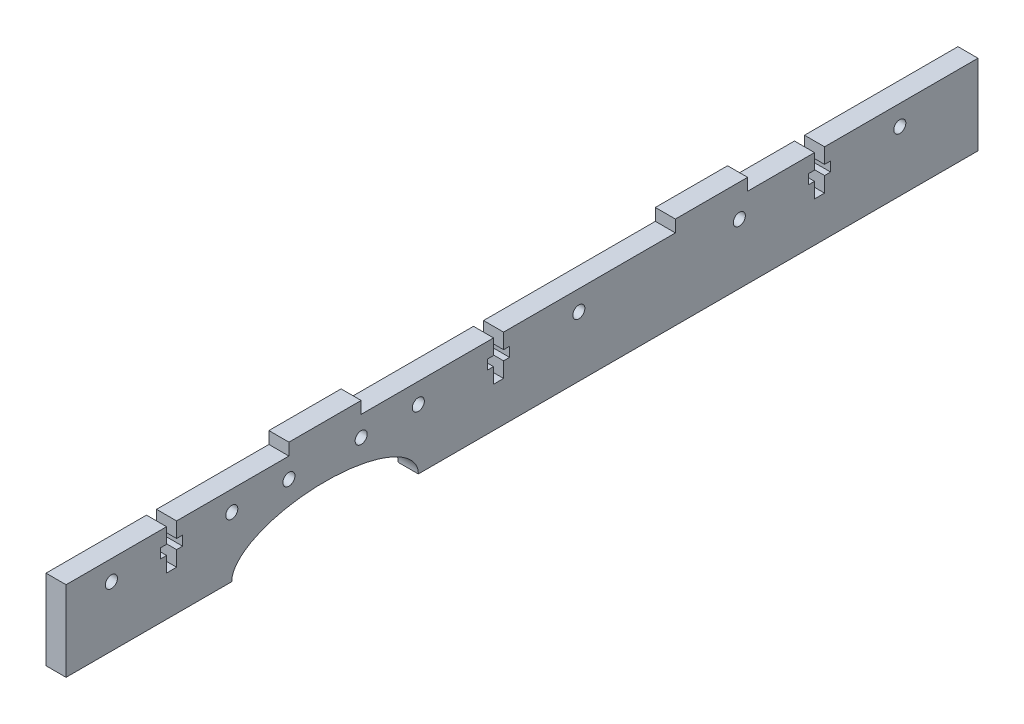
SolidWorks part; units mm, degrees
material "PMMA"
ref_plane "Front Plane" through (0, 0, 0) normal (0, 0, 1) x (1, 0, 0)
ref_plane "Top Plane" through (0, 0, 0) normal (0, 1, 0) x (1, 0, 0)
ref_plane "Right Plane" through (0, 0, 0) normal (1, 0, 0) x (0, 0, -1)
sketch "Schizzo1" plane through (0, 0, 0) normal (1, 0, 0) x (0, 0, -1)
  line L0 (-115.445, 5) -> (-2.745, 5) construction
  line L1 (-113.645, -10) -> (113.645, -10)
  line L2 (-113.645, -10) -> (-113.645, 10)
  line L3 (-113.645, 10) -> (-58.095, 10)
  line L4 (113.645, -10) -> (113.645, 10)
  line L5 (-49.095, 10) -> (-49.095, -10) construction
  line L6 (-58.095, 10) -> (-58.095, 13)
  line L7 (-58.095, 13) -> (-40.095, 13)
  line L8 (-40.095, 13) -> (-40.095, 10)
  line L9 (-40.095, 10) -> (113.645, 10)
  line L10 (-113.645, 10) -> (113.645, -10) construction
  point P8 (0, 0)
  dimension "D2" = 20
  dimension "D3" = 9
  dimension "D4" = 9
  dimension "D5" = 3
  dimension "D1" = 55.55
  dimension "D6" = 5
  dimension "D8" = 153.74
extrude "Estrusione-Estrusione1" add sketch "Schizzo1" along normal blind 5
sketch "Schizzo3" plane through (0, 0, 0) normal (1, 0, 0) x (0, 0, -1)
  line L1 (-40.095, 13) -> (-58.095, 13) construction
  line L2 (-113.645, -10) -> (113.645, -10) construction
  line L4 (-49.095, 13) -> (-49.095, -10) construction
  line L5 (-113.645, 5) -> (113.645, 5) construction
  line L10 (-58.095, 10) -> (-113.645, 10) construction
  line L11 (-113.645, 10) -> (-113.645, -10) construction
  line L12 (113.645, -10) -> (113.645, 10) construction
  circle A0 centre (-58.095, 5) radius 1.5
  circle A1 centre (-72.345, 5) radius 1.5
  circle A2 centre (-40.095, 5) radius 1.5
  circle A3 centre (-25.845, 5) radius 1.5
  circle A4 centre (14.155, 5) radius 1.5
  circle A5 centre (54.155, 5) radius 1.5
  circle A6 centre (94.155, 5) radius 1.5
  circle A7 centre (-102.345, 5) radius 1.5
  ellipse E0 centre (-49.095, -10) end of major axis (-25.845, -10) minor radius 10
  dimension "D3" = 3
  dimension "D6" = 3
  dimension "D4" = 4
  dimension "D1" = 9
  dimension "D2" = 23.25
  dimension "D5" = 2
  dimension "D8" = 5
extrude "Taglio-Estrusione1" cut sketch "Schizzo3" along direction (-1, 0, 0) on the side of the normal through all
sketch "Schizzo5" plane through (0, 0, 0) normal (1, 0, 0) x (0, 0, -1)
  line L0 (-100.845, 5) -> (-73.845, 5) construction
  line L1 (-24.345, 5) -> (12.655, 5) construction
  line L2 (55.655, 5) -> (92.655, 5) construction
  line L3 (-5.845, 0) -> (-5.845, 10) construction
  line L4 (-87.345, 0) -> (-87.345, 10) construction
  line L5 (-88.595, 0) -> (-88.595, 3.8)
  line L6 (-88.595, 3.8) -> (-90.095, 3.8)
  line L7 (-90.095, 3.8) -> (-90.095, 6.2)
  line L8 (-90.095, 6.2) -> (-88.595, 6.2)
  line L9 (-88.595, 6.2) -> (-88.595, 10)
  line L10 (-88.595, 10) -> (-86.095, 10)
  line L11 (-86.095, 10) -> (-86.095, 6.2)
  line L12 (-86.095, 6.2) -> (-84.595, 6.2)
  line L13 (-84.595, 6.2) -> (-84.595, 3.8)
  line L14 (-84.595, 3.8) -> (-86.095, 3.8)
  line L15 (-86.095, 3.8) -> (-86.095, 0)
  line L16 (-86.095, 0) -> (-88.595, 0)
  line L17 (-58.095, 10) -> (-113.645, 10) construction
  line L18 (-7.095, 0) -> (-7.095, 3.8)
  line L19 (-7.095, 3.8) -> (-8.595, 3.8)
  line L20 (-8.595, 3.8) -> (-8.595, 6.2)
  line L21 (-8.595, 6.2) -> (-7.095, 6.2)
  line L22 (-7.095, 6.2) -> (-7.095, 10)
  line L23 (-7.095, 10) -> (-4.595, 10)
  line L24 (-4.595, 10) -> (-4.595, 6.2)
  line L25 (-4.595, 6.2) -> (-3.095, 6.2)
  line L26 (-3.095, 6.2) -> (-3.095, 3.8)
  line L27 (-3.095, 3.8) -> (-4.595, 3.8)
  line L28 (-4.595, 3.8) -> (-4.595, 0)
  line L29 (-4.595, 0) -> (-7.095, 0)
  line L30 (113.645, 10) -> (-40.095, 10) construction
  line L31 (74.155, 0) -> (74.155, 10) construction
  line L32 (72.905, 0) -> (72.905, 3.8)
  line L33 (72.905, 3.8) -> (71.405, 3.8)
  line L34 (71.405, 3.8) -> (71.405, 6.2)
  line L35 (71.405, 6.2) -> (72.905, 6.2)
  line L36 (72.905, 6.2) -> (72.905, 10)
  line L37 (72.905, 10) -> (75.405, 10)
  line L38 (75.405, 10) -> (75.405, 6.2)
  line L39 (75.405, 6.2) -> (76.905, 6.2)
  line L40 (76.905, 6.2) -> (76.905, 3.8)
  line L41 (76.905, 3.8) -> (75.405, 3.8)
  line L42 (75.405, 3.8) -> (75.405, 0)
  line L43 (75.405, 0) -> (72.905, 0)
  line L44 (113.645, 10) -> (-40.095, 10) construction
  line L45 (-113.645, 10) -> (-113.645, -10) construction
  circle A0 centre (-102.345, 5) radius 1.5 construction
  circle A1 centre (-72.345, 5) radius 1.5 construction
  circle A2 centre (-25.845, 5) radius 1.5 construction
  circle A3 centre (14.155, 5) radius 1.5 construction
  circle A4 centre (54.155, 5) radius 1.5 construction
  circle A5 centre (94.155, 5) radius 1.5 construction
  point P39 (-87.345, 5)
  point P40 (-87.345, 0)
  point P53 (-5.845, 0)
  point P55 (-5.845, 5)
  point P72 (74.155, 0)
  point P73 (74.155, 5)
  dimension "D1" = 2.4
  dimension "D2" = 10
  dimension "D3" = 90
  dimension "D4" = 90
  dimension "D5" = 2.5
  dimension "D6" = 3.8
  dimension "D7" = 5.5
  dimension "D8" = 2.4
  dimension "D9" = 10
  dimension "D10" = 90
  dimension "D11" = 90
  dimension "D12" = 2.5
  dimension "D13" = 3.8
  dimension "D14" = 5.5
  dimension "D15" = 2.4
  dimension "D16" = 10
  dimension "D17" = 90
  dimension "D18" = 90
  dimension "D19" = 2.5
  dimension "D20" = 3.8
  dimension "D21" = 5.5
  dimension "D22" = 26.3
  dimension "D23" = 107.8
  dimension "D24" = 187.8
extrude "Taglio-Estrusione2" cut sketch "Schizzo5" along normal through all
sketch "Schizzo6" plane through (0, 10, 0) normal (0, 1, 0) x (1, 0, 0)
  line L0 (5, 72.905) -> (5, -4.595) construction
  line L1 (0, 56.225) -> (5, 56.225)
  line L2 (0, 56.225) -> (0, 38.225)
  line L3 (0, 38.225) -> (5, 38.225)
  line L4 (5, 56.225) -> (5, 38.225)
  line L5 (0, 72.905) -> (0, -4.595) construction
  line L6 (5, 113.645) -> (0, 113.645) construction
  point P8 (2.5, 113.645)
  dimension "D1" = 18
  dimension "D2" = 57.42
extrude "Estrusione-Estrusione2" add sketch "Schizzo6" along normal blind 3
sketch "Schizzo7" plane through (5, 0, 0) normal (1, 0, 0) x (0, 0, -1)
  line L0 (-84.595, 3.8) -> (-84.595, 6.2) construction
  circle A0 centre (-90.095, 6.2) radius 0.25
  circle A1 centre (-84.595, 6.2) radius 0.25
  circle A2 centre (-8.595, 6.2) radius 0.25
  circle A3 centre (-3.095, 6.2) radius 0.25
  circle A4 centre (71.405, 6.2) radius 0.25
  circle A5 centre (76.905, 6.2) radius 0.25
  dimension "D1" = 0.5
  dimension "D2" = 0.5
  dimension "D3" = 0.5
equation "\"Thickness5\"=5"
equation "\"D1@Estrusione-Estrusione1\"=\"Thickness5\""
equation "\"D5@Schizzo1\"=\"Thickness3\""
equation "\"D1@Estrusione-Estrusione2\"=\"Thickness3\""
equation "\"Thickness3\"= 3"
